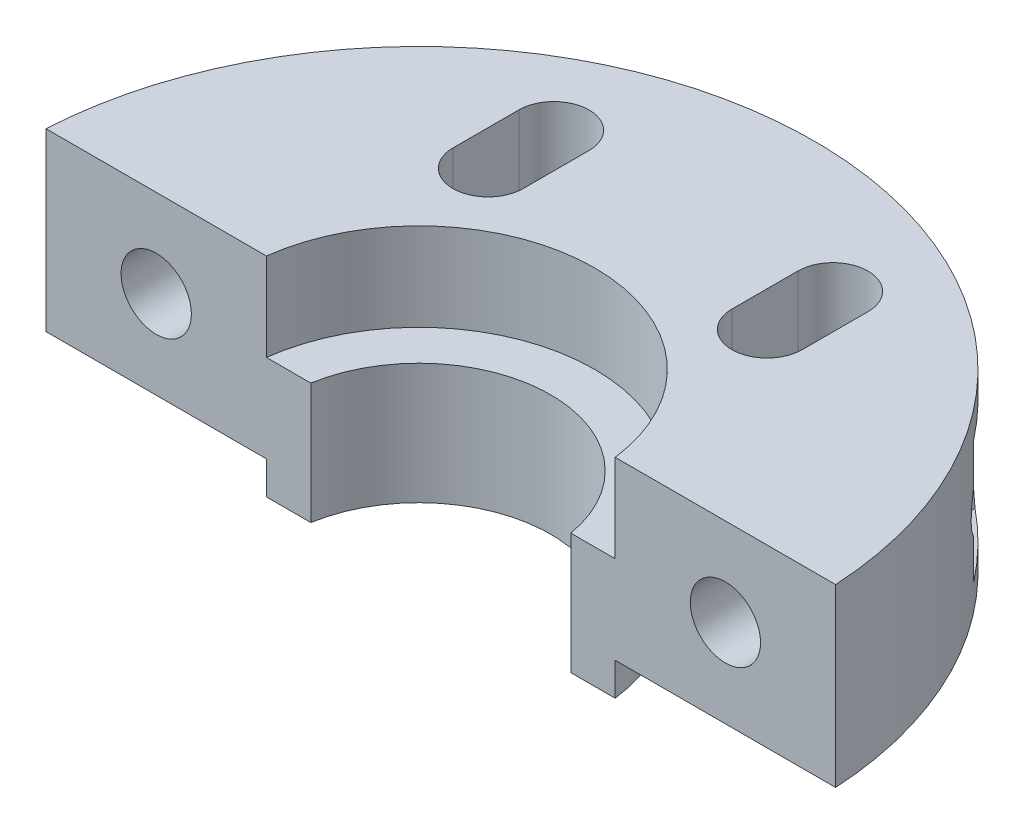
SolidWorks part; units mm, degrees
material "ABS"
ref_plane "Front Plane" through (0, 0, 0) normal (0, 0, 1) x (1, 0, 0)
ref_plane "Top Plane" through (0, 0, 0) normal (0, 1, 0) x (1, 0, 0)
ref_plane "Right Plane" through (0, 0, 0) normal (1, 0, 0) x (0, 0, -1)
sketch "Sketch1" plane through (0, 0, 0) normal (0, 1, 0) x (1, 0, 0)
  line L0 (-7.9509, 12.5) -> (-7.9509, 9.5)
  line L1 (12.7017, 0) -> (6.3509, 11) construction
  line L2 (6.3509, 11) -> (-6.3509, 11) construction
  line L3 (-6.3509, 11) -> (-12.7017, 0) construction
  line L4 (-12.7017, 0) -> (-6.3509, -11) construction
  line L5 (-6.3509, -11) -> (6.3509, -11) construction
  line L6 (6.3509, -11) -> (12.7017, 0) construction
  line L7 (-4.7509, 12.5) -> (-4.7509, 9.5)
  line L8 (4.7509, 12.5) -> (4.7509, 9.5)
  line L9 (7.9509, 12.5) -> (7.9509, 9.5)
  line L10 (-6.3509, 11) -> (-7.9509, 11) construction
  line L11 (6.3509, 11) -> (7.9509, 11) construction
  circle A0 centre (0, 0) radius 8
  circle A1 centre (0, 0) radius 18
  circle A2 centre (0, 0) radius 11 construction
  arc A3 (7.9509, 12.5) -> (4.7509, 12.5) centre (6.3509, 12.5) ccw
  arc A4 (-7.9509, 9.5) -> (-4.7509, 9.5) centre (-6.3509, 9.5) ccw
  arc A6 (4.7509, 9.5) -> (7.9509, 9.5) centre (6.3509, 9.5) ccw
  arc A7 (-4.7509, 12.5) -> (-7.9509, 12.5) centre (-6.3509, 12.5) ccw
  dimension "D1" = 16
  dimension "D2" = 10
  dimension "D3" = 22
  dimension "D4" = 1.6
  dimension "D5" = 3
extrude "Boss-Extrude1" add sketch "Sketch1" along normal blind 8
ref_plane "Plane1" through (0, 4, 0) normal (0, 1, 0) x (1, 0, 0)
sketch "Sketch2" plane through (0, 4, 0) normal (0, 1, 0) x (1, 0, 0)
  circle A0 centre (0, 0) radius 8
  circle A1 centre (0, 0) radius 6
  dimension "D1" = 16
  dimension "D2" = 12
extrude "Boss-Extrude2" add sketch "Sketch2" against normal blind 5.5
sketch "Sketch3" plane through (0, 8, 0) normal (0, 1, 0) x (1, 0, 0)
  line L0 (-20, 1) -> (20, 1)
  line L1 (20, 1) -> (20, -19)
  line L2 (20, -19) -> (-20, -19)
  line L3 (-20, -19) -> (-20, 1)
  line L4 (0, 0) -> (0, 1) construction
  dimension "D1" = 20
  dimension "D2" = 1
  dimension "D3" = 40
extrude "Cut-Extrude1" cut sketch "Sketch3" against normal through all
sketch "Sketch5" plane through (0, 0, -1) normal (0, 0, 1) x (1, 0, 0)
  line L0 (-7.9373, 8) -> (-17.9722, 8) construction
  line L1 (-12.9547, 8) -> (-12.9547, 4) construction
  line L2 (-17.9722, 4) -> (-12.9547, 4) construction
  line L3 (-17.9722, 0) -> (-17.9722, 8) construction
  line L4 (12.9547, 8) -> (12.9547, 4) construction
  line L5 (17.9722, 8) -> (7.9373, 8) construction
  line L6 (12.9547, 4) -> (17.9722, 4) construction
  line L7 (17.9722, 8) -> (17.9722, 0) construction
  circle A0 centre (-12.9547, 4) radius 1.6
  circle A1 centre (12.9547, 4) radius 1.6
  dimension "D1" = 3.2
extrude "Cut-Extrude2" cut sketch "Sketch5" against normal up to next
sketch "Sketch6" plane through (0, 0, -1) normal (0, 0, 1) x (1, 0, 0)
  line L1 (-9.7216, 4) -> (-11.3381, 6.8)
  line L2 (-11.3381, 6.8) -> (-14.5713, 6.8)
  line L3 (-14.5713, 6.8) -> (-16.1879, 4)
  line L4 (-16.1879, 4) -> (-14.5713, 1.2)
  line L5 (-14.5713, 1.2) -> (-11.3381, 1.2)
  line L6 (-11.3381, 1.2) -> (-9.7216, 4)
  line L7 (16.1879, 4) -> (14.5713, 6.8)
  line L8 (14.5713, 6.8) -> (11.3381, 6.8)
  line L9 (11.3381, 6.8) -> (9.7216, 4)
  line L10 (9.7216, 4) -> (11.3381, 1.2)
  line L11 (11.3381, 1.2) -> (14.5713, 1.2)
  line L12 (14.5713, 1.2) -> (16.1879, 4)
  circle A0 centre (-12.9547, 4) radius 2.8 construction
  circle A1 centre (12.9547, 4) radius 2.8 construction
  dimension "D1" = 5.6
extrude "Cut-Extrude3" cut sketch "Sketch6" against normal up to next from offset 10
